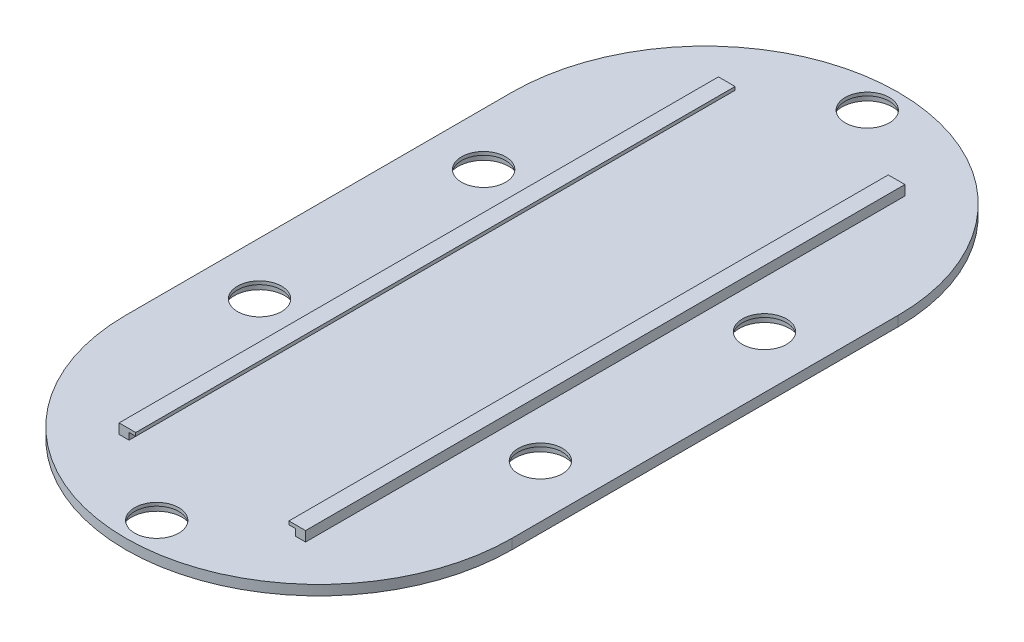
SolidWorks part; units mm, degrees
ref_plane "Front Plane" through (0, 0, 0) normal (0, 0, 1) x (1, 0, 0)
ref_plane "Top Plane" through (0, 0, 0) normal (0, 1, 0) x (1, 0, 0)
ref_plane "Right Plane" through (0, 0, 0) normal (1, 0, 0) x (0, 0, -1)
sketch "Sketch1" plane through (0, 0, 0) normal (0, 1, 0) x (1, 0, 0)
  line L0 (-1000, 0) -> (49000, 0) construction
  line L1 (58, -58) -> (58, 58)
  line L2 (-58, -58) -> (-58, 58)
  circle A0 centre (0, 58) radius 58 construction
  circle A1 centre (0, 106.6995) radius 6.625
  circle A2 centre (42.175, 33.6503) radius 6.625
  circle A3 centre (-42.175, 33.6503) radius 6.625
  circle A4 centre (-42.175, -33.6503) radius 6.625
  circle A5 centre (0, -106.6995) radius 6.625
  circle A6 centre (42.175, -33.6503) radius 6.625
  circle A7 centre (0, -58) radius 58 construction
  arc A8 (58, -58) -> (-58, -58) centre (0, -58) cw
  arc A9 (-58, 58) -> (58, 58) centre (0, 58) cw
  point P12 (0, 58)
  dimension "D1" = 116
  dimension "D2" = 13.25
  dimension "D4" = 84.35
  dimension "D3" = 3
extrude "Boss-Extrude1" add sketch "Sketch1" along normal blind 3
sketch "Sketch2" plane through (0, 0, 0) normal (0, -1, 0) x (1, 0, 0)
  circle A21 centre (42.175, -33.6503) radius 7.6
  circle A22 centre (-42.175, -33.6503) radius 7.6
  circle A23 centre (0, -106.6995) radius 7.6
  circle A24 centre (42.175, 33.6503) radius 7.6
  circle A25 centre (0, 106.6995) radius 7.6
  circle A26 centre (-42.175, 33.6503) radius 7.6
  dimension "D1" = 15.2
extrude "Cut-Extrude1" cut sketch "Sketch2" against normal blind 2
sketch "Sketch3" plane through (0, 0, 0) normal (0, 0, 1) x (1, 0, 0)
  line L0 (58, 3) -> (-58, 3) construction
  line L1 (-23, 5) -> (-25, 5)
  line L2 (28, 3) -> (28, 6)
  line L3 (28, 6) -> (23, 6)
  line L4 (23, 6) -> (23, 5)
  line L5 (23, 5) -> (25, 5)
  line L6 (25, 5) -> (25, 3)
  line L7 (0, 0) -> (0, 25.874) construction
  line L8 (25, 3) -> (28, 3)
  line L9 (-23, 6) -> (-23, 5)
  line L10 (-28, 6) -> (-23, 6)
  line L11 (-28, 3) -> (-28, 6)
  line L12 (-25, 3) -> (-28, 3)
  line L13 (-25, 5) -> (-25, 3)
  point P17 (26.2775, 3)
  dimension "D1" = 25
  dimension "D2" = 3
  dimension "D3" = 2
  dimension "D4" = 1
  dimension "D5" = 2
extrude "Boss-Extrude2" add sketch "Sketch3" along normal mid plane 180
